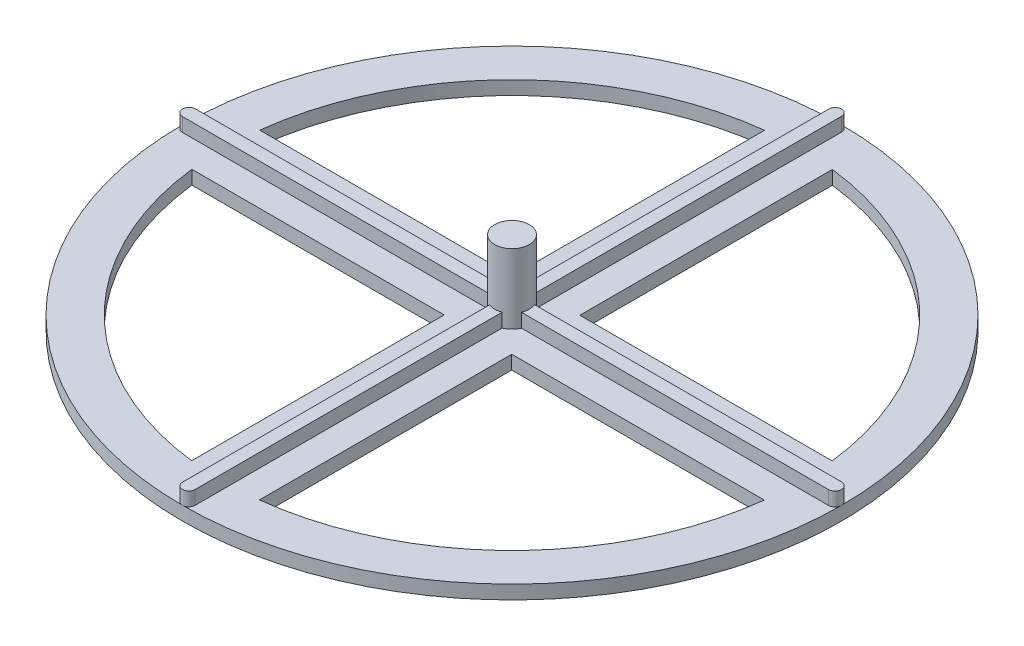
SolidWorks part; units mm, degrees
ref_plane "Front Plane" through (0, 0, 0) normal (0, 0, 1) x (1, 0, 0)
ref_plane "Top Plane" through (0, 0, 0) normal (0, 1, 0) x (1, 0, 0)
ref_plane "Right Plane" through (0, 0, 0) normal (1, 0, 0) x (0, 0, -1)
sketch "Sketch1" plane through (0, 0, 0) normal (0, 1, 0) x (1, 0, 0)
  circle A0 centre (0, 0) radius 76.2
  dimension "D1" = 152.4
extrude "Boss-Extrude1" add sketch "Sketch1" along normal blind 3.175
sketch "Sketch2" plane through (0, 3.175, 0) normal (0, 1, 0) x (1, 0, 0)
  line L0 (0, -76.2) -> (0, 76.2)
  line L1 (-76.2, 0) -> (76.2, 0)
  line L2 (-74.676, 0) -> (74.676, 0) construction
  line L3 (-74.676, 1.524) -> (74.676, 1.524)
  line L4 (-74.676, -1.524) -> (74.676, -1.524)
  line L5 (0, 74.7395) -> (0, -74.7395) construction
  line L6 (1.4605, 74.7395) -> (1.4605, -74.7395)
  line L7 (-1.4605, 74.7395) -> (-1.4605, -74.7395)
  circle A0 centre (0, 0) radius 76.2 construction
  arc A1 (-74.676, 1.524) -> (-74.676, -1.524) centre (-74.676, 0) ccw
  arc A2 (74.676, -1.524) -> (74.676, 1.524) centre (74.676, 0) ccw
  arc A3 (1.4605, 74.7395) -> (-1.4605, 74.7395) centre (0, 74.7395) ccw
  arc A4 (-1.4605, -74.7395) -> (1.4605, -74.7395) centre (0, -74.7395) ccw
  point P7 (0, 0)
  point P11 (0, 0)
  point P12 (0, 0)
  point P19 (0, 0)
  dimension "D1" = 3.048
  dimension "D2" = 2.921
extrude "Boss-Extrude2" add sketch "Sketch2" along normal blind 3.175 contours L7 A4 L6 A3 | L4 A1 L3 A2
sketch "Sketch3" plane through (0, 6.35, 0) normal (0, 1, 0) x (1, 0, 0)
  circle A0 centre (0, 0) radius 4
  dimension "D1" = 8
extrude "Boss-Extrude3" add sketch "Sketch3" along normal blind 12.954 and the other way up to surface (6.35 mm away)
sketch "Sketch4" plane through (0, 3.175, 0) normal (0, 1, 0) x (1, 0, 0)
  line L0 (-7.8105, 7.874) -> (-39.5605, 7.874)
  line L1 (-74.676, 1.524) -> (-3.6983, 1.524) construction
  line L2 (-1.4605, 74.7395) -> (-1.4605, 3.7238) construction
  line L3 (-7.8105, 7.874) -> (-7.8105, 63.0178)
  line L4 (-39.5605, 7.874) -> (-63.0099, 7.874)
  line L5 (-7.8105, 63.0178) -> (-7.8105, 66.2159)
  line L6 (-63.0099, 7.874) -> (-66.2084, 7.874)
  line L7 (7.874, 63.0099) -> (7.874, 66.2084)
  line L8 (7.874, 39.5605) -> (7.874, 63.0099)
  line L9 (7.874, 7.8105) -> (7.874, 39.5605)
  line L10 (7.874, 7.8105) -> (63.0178, 7.8105)
  line L11 (63.0178, 7.8105) -> (66.2159, 7.8105)
  line L12 (63.0099, -7.874) -> (66.2084, -7.874)
  line L13 (39.5605, -7.874) -> (63.0099, -7.874)
  line L14 (7.8105, -7.874) -> (39.5605, -7.874)
  line L15 (7.8105, -7.874) -> (7.8105, -63.0178)
  line L16 (7.8105, -63.0178) -> (7.8105, -66.2159)
  line L17 (-7.874, -63.0099) -> (-7.874, -66.2084)
  line L18 (-7.874, -39.5605) -> (-7.874, -63.0099)
  line L19 (-7.874, -7.8105) -> (-7.874, -39.5605)
  line L20 (-7.874, -7.8105) -> (-63.0178, -7.8105)
  line L21 (-63.0178, -7.8105) -> (-66.2159, -7.8105)
  arc A2 (-7.8105, 66.2159) -> (-66.2084, 7.874) centre (0, 0) ccw
  arc A3 (66.2159, 7.8105) -> (7.874, 66.2084) centre (0, 0) ccw
  arc A4 (7.8105, -66.2159) -> (66.2084, -7.874) centre (0, 0) ccw
  arc A5 (-66.2159, -7.8105) -> (-7.874, -66.2084) centre (0, 0) ccw
  point P34 (0, 0)
  dimension "D1" = 6.35
  dimension "D3" = 4
  dimension "D2" = 6.35
extrude "Cut-Extrude1" cut sketch "Sketch4" against normal through all
